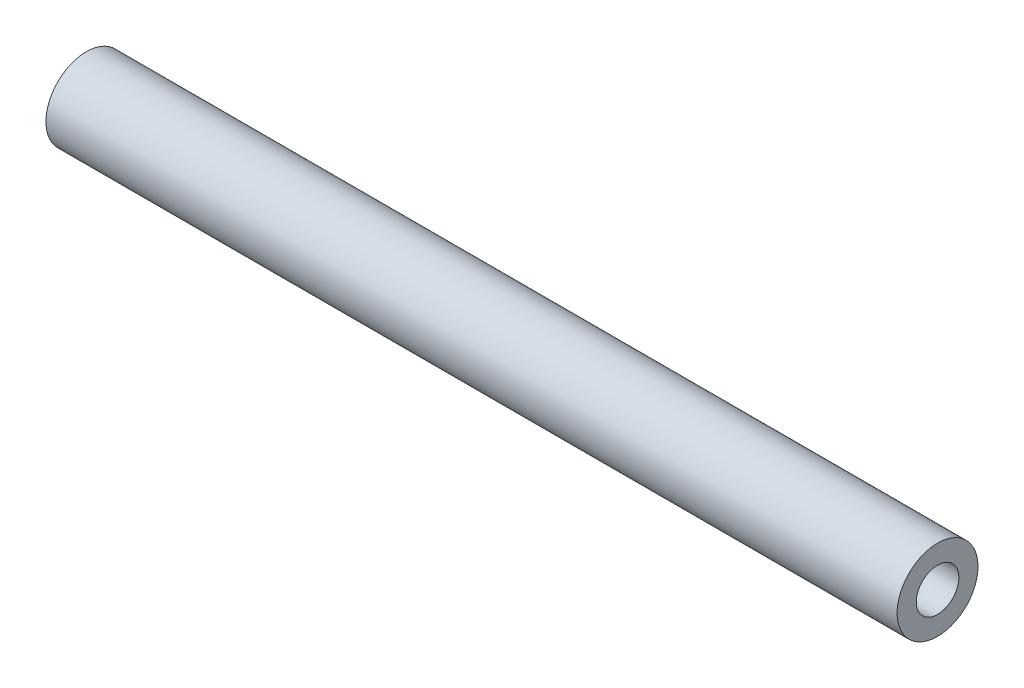
SolidWorks part; units mm, degrees
ref_plane "Front Plane" through (0, 0, 0) normal (0, 0, 1) x (1, 0, 0)
ref_plane "Top Plane" through (0, 0, 0) normal (0, 1, 0) x (1, 0, 0)
ref_plane "Right Plane" through (0, 0, 0) normal (1, 0, 0) x (0, 0, -1)
sketch "Sketch1" plane through (0, 0, 0) normal (1, 0, 0) x (0, 0, -1)
  circle A0 centre (0, 0) radius 8.001
  dimension "D1" = 16.002
extrude "Boss-Extrude1" add sketch "Sketch1" along normal blind 168.402
hole_wizard "3/8-24 Tapped Hole1" positions "Sketch2" profile "Sketch3" tap size "3/8-24" standard "ANSI Inch"
sketch "Sketch2" plane through (168.402, 0, 0) normal (1, 0, 0) x (0, 0, -1)
  point P0 (0, 0)
sketch "Sketch3" plane through (168.402, 0, 0) normal (0, 1, 0) x (0, 0, -1)
  line L0 (0, 0) -> (0, 24.8855)
  line L1 (0, 24.8855) -> (4.2164, 22.352)
  line L2 (4.2164, 22.352) -> (4.2164, 0)
  line L5 (4.2164, 0) -> (0, 0)
  line L10 (0, 24.8855) -> (-4.2164, 22.352) construction
  line L11 (0, -6.35) -> (0, 107.95) construction
  dimension "Tap Drill Dia." = 8.4328
  dimension "Tap Drill Depth" = 22.352
  dimension "Drill Angle" = 118
cosmetic thread "Hole Thread1" parameters "D1"=19.05, "D2"=9.525
